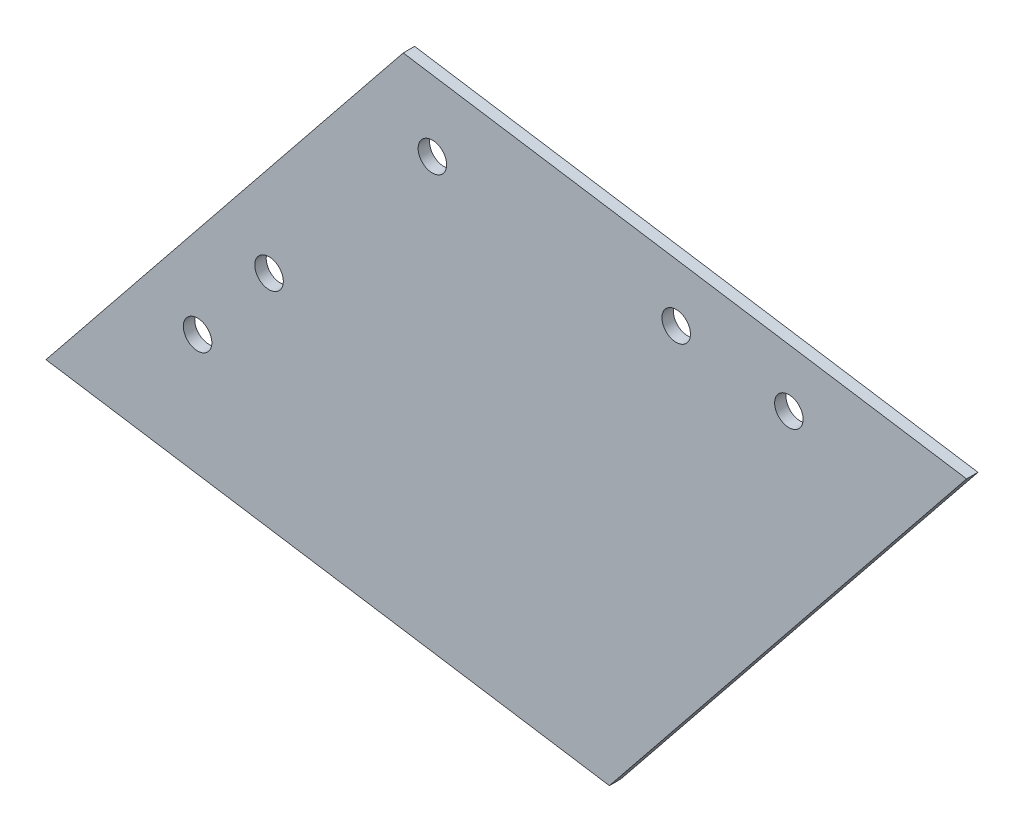
SolidWorks part; units mm, degrees
ref_plane "Front Plane" through (0, 0, 0) normal (0, 0, 1) x (1, 0, 0)
ref_plane "Top Plane" through (0, 0, 0) normal (0, 1, 0) x (1, 0, 0)
ref_plane "Right Plane" through (0, 0, 0) normal (1, 0, 0) x (0, 0, -1)
sketch "Sketch1" plane through (0, 0, 0) normal (0, 0, 1) x (1, 0, 0)
  line L0 (0, 0) -> (62.6628, 77.9319)
  line L1 (62.6628, 77.9319) -> (161.4851, 62.6302)
  line L2 (161.4851, 62.6302) -> (98.8224, -15.3016)
  line L3 (0, 0) -> (98.8224, -15.3016)
  dimension "D1" = 100
  dimension "D2" = 100
  dimension "D3" = 120
  dimension "D4" = 100
extrude "Boss-Extrude1" add sketch "Sketch1" along normal blind 2
sketch "Sketch2" plane through (0, 0, 0) normal (0, 0, -1) x (-1, 0, 0)
  line L0 (-31.3314, 38.9659) -> (-39.1246, 32.6997)
  line L1 (-62.6628, 77.9319) -> (0, 0) construction
  circle A0 centre (-39.1246, 32.6997) radius 2.5
  dimension "D1" = 10
extrude "Cut-Extrude1" cut sketch "Sketch2" against normal blind 6 contours A0
sketch "Sketch3" plane through (0, 0, 0) normal (0, 0, -1) x (-1, 0, 0)
  line L0 (0, 0) -> (-18.7988, 23.3796)
  line L1 (-62.6628, 77.9319) -> (0, 0) construction
  line L2 (-18.7988, 23.3796) -> (-26.592, 17.1133)
  circle A0 centre (-26.592, 17.1133) radius 2.5
  dimension "D1" = 30
  dimension "D2" = 10
extrude "Cut-Extrude2" cut sketch "Sketch3" against normal blind 6 contours A0
sketch "Sketch4" plane through (0, 0, 0) normal (0, 0, -1) x (-1, 0, 0)
  line L0 (-161.4851, 62.6302) -> (-131.8384, 67.2207)
  line L1 (-161.4851, 62.6302) -> (-62.6628, 77.9319) construction
  line L2 (-131.8384, 67.2207) -> (-130.3083, 57.3385)
  circle A0 centre (-130.3083, 57.3385) radius 2.5
  dimension "D1" = 30
  dimension "D2" = 90
  dimension "D3" = 10
extrude "Cut-Extrude3" cut sketch "Sketch4" against normal blind 6 contours A0
sketch "Sketch5" plane through (0, 0, 0) normal (0, 0, -1) x (-1, 0, 0)
  line L0 (-161.4851, 62.6302) -> (-112.074, 70.2811)
  line L1 (-161.4851, 62.6302) -> (-62.6628, 77.9319) construction
  line L2 (-112.074, 70.2811) -> (-110.5438, 60.3988)
  circle A0 centre (-110.5438, 60.3988) radius 2.5
  dimension "D1" = 10
extrude "Cut-Extrude4" cut sketch "Sketch5" against normal blind 6 contours A0
sketch "Sketch6" plane through (0, 0, 0) normal (0, 0, -1) x (-1, 0, 0)
  line L0 (-62.6628, 77.9319) -> (-67.7765, 64.7467)
  line L1 (-62.6628, 77.9319) -> (0, 0) construction
  circle A0 centre (-67.7765, 64.7467) radius 2.5
  dimension "D1" = 60
  dimension "D2" = 14.1421
extrude "Cut-Extrude5" cut sketch "Sketch6" against normal blind 6 contours A0
